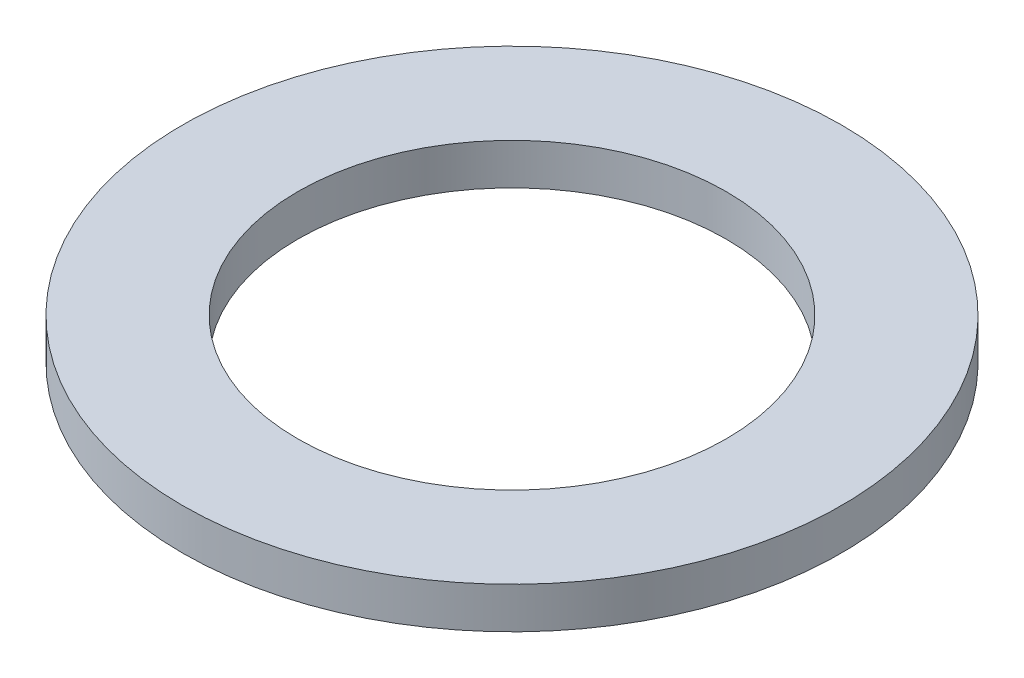
SolidWorks part; units mm, degrees
ref_plane "Спереди" through (0, 0, 0) normal (0, 0, 1) x (1, 0, 0)
ref_plane "Сверху" through (0, 0, 0) normal (0, 1, 0) x (1, 0, 0)
ref_plane "Справа" through (0, 0, 0) normal (1, 0, 0) x (0, 0, -1)
sketch "Эскиз1" plane through (0, 0, 0) normal (0, 1, 0) x (1, 0, 0)
  circle A0 centre (0, 0) radius 4
  circle A1 centre (0, 0) radius 2.6
extrude "Бобышка-Вытянуть1" add sketch "Эскиз1" along normal blind 0.5
